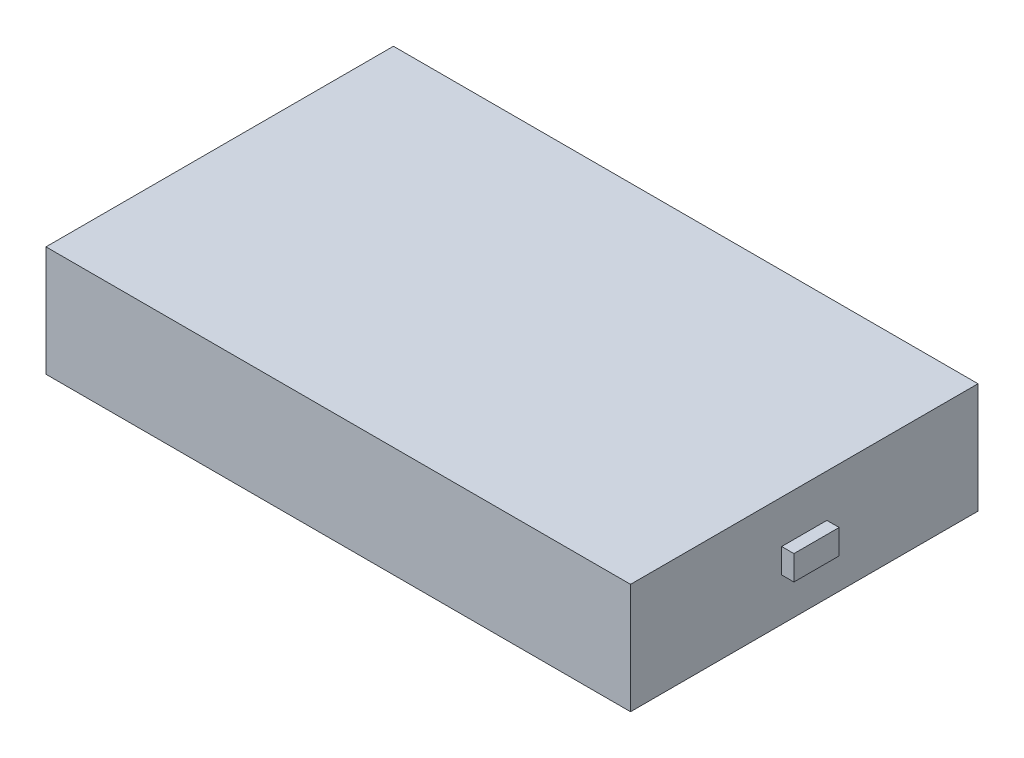
SolidWorks part; units mm, degrees
ref_plane "Front Plane" through (0, 0, 0) normal (0, 0, 1) x (1, 0, 0)
ref_plane "Top Plane" through (0, 0, 0) normal (0, 1, 0) x (1, 0, 0)
ref_plane "Right Plane" through (0, 0, 0) normal (1, 0, 0) x (0, 0, -1)
sketch "Sketch1" plane through (0, 0, 0) normal (0, 1, 0) x (1, 0, 0)
  line L1 (71.5, -42.5) -> (-71.5, -42.5)
  line L2 (71.5, -42.5) -> (71.5, 42.5)
  line L3 (71.5, 42.5) -> (-71.5, 42.5)
  line L4 (-71.5, -42.5) -> (-71.5, 42.5)
  line L5 (71.5, -42.5) -> (-71.5, 42.5) construction
  line L6 (71.5, 42.5) -> (-71.5, -42.5) construction
  point P0 (0, 0)
  dimension "D1" = 143
  dimension "D2" = 85
extrude "Boss-Extrude1" add sketch "Sketch1" along normal blind 27
sketch "Sketch2" plane through (71.5, 0, 0) normal (1, 0, 0) x (0, 0, -1)
  line L1 (5.5326, 10.5051) -> (-5.5326, 10.5051)
  line L2 (5.5326, 10.5051) -> (5.5326, 16.5295)
  line L3 (5.5326, 16.5295) -> (-5.5326, 16.5295)
  line L4 (-5.5326, 10.5051) -> (-5.5326, 16.5295)
  line L5 (5.5326, 10.5051) -> (-5.5326, 16.5295) construction
  line L6 (5.5326, 16.5295) -> (-5.5326, 10.5051) construction
  point P0 (0, 13.5173)
extrude "Boss-Extrude2" add sketch "Sketch2" along normal blind 3
